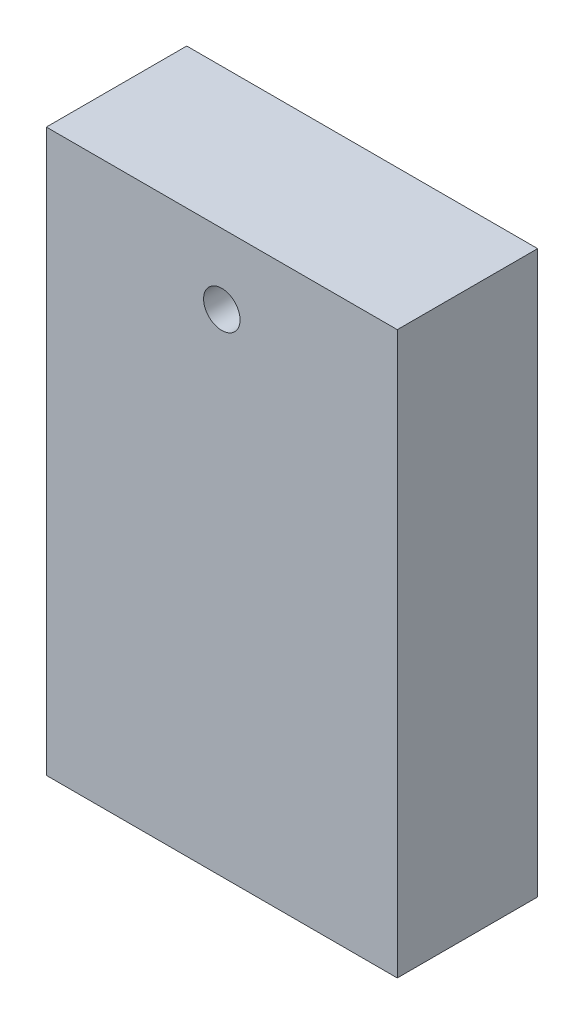
SolidWorks part; units mm, degrees
ref_plane "Front Plane" through (0, 0, 0) normal (0, 0, 1) x (1, 0, 0)
ref_plane "Top Plane" through (0, 0, 0) normal (0, 1, 0) x (1, 0, 0)
ref_plane "Right Plane" through (0, 0, 0) normal (1, 0, 0) x (0, 0, -1)
sketch "Sketch1" plane through (0, 0, 0) normal (0, 0, 1) x (1, 0, 0)
  line L0 (-12.5, 15) -> (12.5, 15) construction
  line L1 (-12.5, 20) -> (12.5, 20)
  line L2 (-12.5, 20) -> (-12.5, -20)
  line L3 (-12.5, -20) -> (12.5, -20)
  line L4 (12.5, 20) -> (12.5, -20)
  line L5 (-12.5, 20) -> (12.5, -20) construction
  line L6 (-12.5, -20) -> (12.5, 20) construction
  circle A0 centre (0, 15) radius 1.3
  circle A1 centre (0, 15) radius 28.5 construction
  point P0 (0, 0)
  point P6 (12.5, 0)
  point P7 (0, 0)
  dimension "D3" = 2.6
  dimension "D5" = 57
  dimension "D1" = 40
  dimension "D2" = 25
  dimension "D4" = 5
extrude "Boss-Extrude1" add sketch "Sketch1" along normal blind 10
